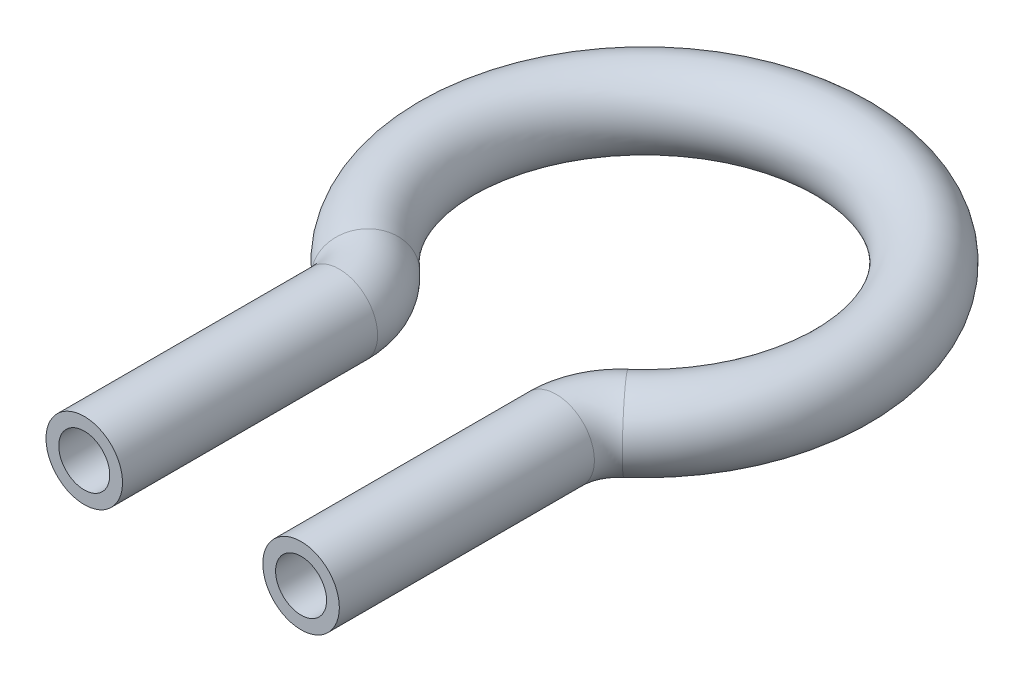
SolidWorks part; units mm, degrees
ref_plane "Front Plane" through (0, 0, 0) normal (0, 0, 1) x (1, 0, 0)
ref_plane "Top Plane" through (0, 0, 0) normal (0, 1, 0) x (1, 0, 0)
ref_plane "Right Plane" through (0, 0, 0) normal (1, 0, 0) x (0, 0, -1)
sketch "Sketch1" plane through (0, 0, 0) normal (0, 1, 0) x (1, 0, 0)
  line L1 (8.5, -15.4272) -> (8.5, -35.4272)
  line L2 (-8.5, -15.4272) -> (-8.5, -35.4272)
  arc A0 (-10.2073, -11.6645) -> (10.2073, -11.6645) centre (0, 0) cw
  arc A1 (10.2073, -11.6645) -> (8.5, -15.4272) centre (13.5, -15.4272) ccw
  arc A2 (-10.2073, -11.6645) -> (-8.5, -15.4272) centre (-13.5, -15.4272) cw
  dimension "D1" = 15.5
  dimension "D3" = 5
  dimension "D4" = 5
  dimension "D2" = 20
  dimension "D5" = 17
ref_plane "Plane1" through (-8.5, 0, 35.4272) normal (0, 0, -1) x (-1, 0, 0)
sketch "Sketch2" plane through (-8.5, 0, 35.4272) normal (0, 0, -1) x (-1, 0, 0)
  circle A0 centre (0, 0) radius 3
  circle A1 centre (0, 0) radius 2
  dimension "D1" = 6
  dimension "D2" = 4
sweep "Sweep1" add profiles "Sketch2" path "Sketch1"
